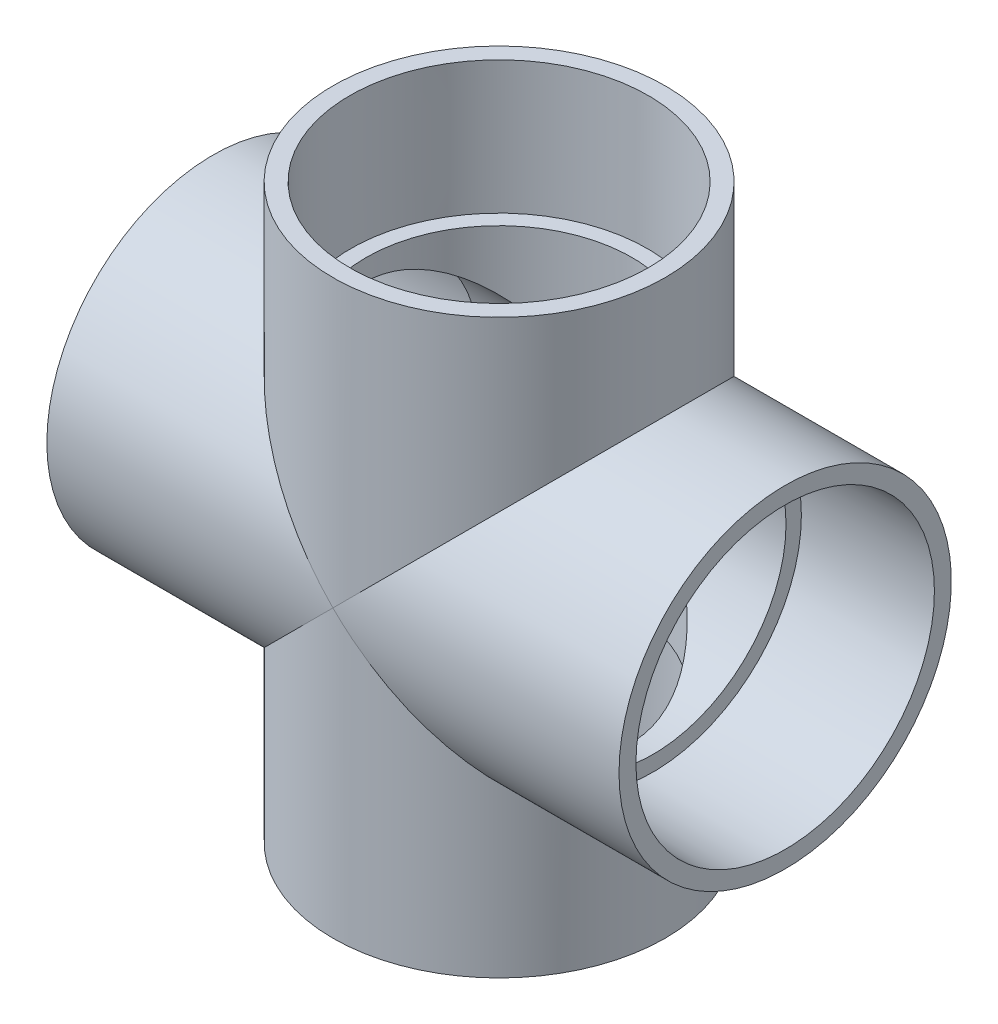
SolidWorks part; units mm, degrees
material "PVC Rigid"
ref_plane "Front Plane" through (0, 0, 0) normal (0, 0, 1) x (1, 0, 0)
ref_plane "Top Plane" through (0, 0, 0) normal (0, 1, 0) x (1, 0, 0)
ref_plane "Right Plane" through (0, 0, 0) normal (1, 0, 0) x (0, 0, -1)
sketch "Sketch0" plane through (0, 0, 0) normal (0, 0, 1) x (1, 0, 0)
  line L0 (-109.982, 0) -> (0, 0) construction
  line L1 (0, 0) -> (0, 109.982) construction
  line L2 (-59.182, 0) -> (0, 0) construction
  line L3 (0, 0) -> (0, 59.182) construction
  line L4 (-109.982, 63.881) -> (-109.982, -63.881) construction
  line L5 (-59.182, 57.0357) -> (-109.982, 57.3786) construction
  line L6 (-59.182, 57.0357) -> (-59.182, -57.0357) construction
  line L7 (-59.182, -57.0357) -> (-109.982, -57.3786) construction
  line L8 (-109.982, 57.3786) -> (-109.982, -57.3786) construction
  line L9 (-63.881, 109.982) -> (63.881, 109.982) construction
  line L10 (-57.3786, 109.982) -> (57.3786, 109.982) construction
  line L11 (57.3786, 109.982) -> (57.0357, 59.182) construction
  line L12 (57.0357, 59.182) -> (-57.0357, 59.182) construction
  line L13 (-57.0357, 59.182) -> (-57.3786, 109.982) construction
  line L14 (-59.182, 51.1302) -> (-59.182, -51.1302) construction
  line L15 (-109.982, 0) -> (-59.182, 0) construction
  line L16 (0, 109.982) -> (0, 59.182) construction
  line L17 (0, 0) -> (59.182, 0) construction
  line L18 (-51.1302, 59.182) -> (51.1302, 59.182) construction
  line L19 (59.182, 0) -> (109.982, 0) construction
  line L20 (0, 0) -> (0, -59.182) construction
  line L21 (0, -59.182) -> (0, -109.982) construction
  dimension "H" = 109.982
  dimension "G" = 59.182
  dimension "M" = 127.762
  dimension "OD A" = 114.7572
  dimension "OD B" = 114.0714
  dimension "ID" = 102.2604
sketch "Sketch1" plane through (0, 0, 0) normal (0, 0, 1) x (1, 0, 0)
  line L0 (-109.982, 0) -> (0, 0) construction
  line L1 (-109.982, 0) -> (0, 0) construction
  line L2 (0, 0) -> (0, -63.881) construction
  line L3 (-109.982, -63.881) -> (-59.182, -63.881)
  line L4 (-109.982, -63.881) -> (-109.982, -57.3786)
  line L5 (-109.982, -57.3786) -> (-59.182, -57.0357)
  line L6 (-59.182, -63.881) -> (-59.182, -57.0357)
  line L7 (-59.182, -63.881) -> (0, -63.881) construction
  line L8 (109.982, -57.3786) -> (59.182, -57.0357)
  line L9 (109.982, -63.881) -> (109.982, -57.3786)
  line L10 (59.182, -63.881) -> (59.182, -57.0357)
  line L11 (109.982, -63.881) -> (59.182, -63.881)
revolve "Revolve1" add sketch "Sketch1" angle 360 about L1
sketch "Sketch2" plane through (0, 0, 0) normal (0, 0, 1) x (1, 0, 0)
  line L0 (57.3786, 109.982) -> (57.0357, 59.182)
  line L1 (57.0357, 59.182) -> (63.881, 59.182)
  line L2 (63.881, 59.182) -> (63.881, 109.982)
  line L3 (63.881, 109.982) -> (57.3786, 109.982)
  line L4 (0, 0) -> (0, 109.982) construction
  line L5 (0, 0) -> (0, 109.982) construction
  line L6 (0, 0) -> (59.182, 0) construction
  line L7 (63.881, -109.982) -> (57.3786, -109.982)
  line L8 (63.881, -59.182) -> (63.881, -109.982)
  line L9 (57.0357, -59.182) -> (63.881, -59.182)
  line L10 (57.3786, -109.982) -> (57.0357, -59.182)
revolve "Revolve2" add sketch "Sketch2" angle 360 about L5
sketch "Sketch3" plane through (-59.182, 0, 0) normal (1, 0, 0) x (0, 0, -1)
  circle A0 centre (0, 0) radius 51.1302
  circle A1 centre (0, 0) radius 63.881
sketch "Sketch4" plane through (-59.182, 0, 0) normal (1, 0, 0) x (0, 0, -1)
  circle A0 centre (0, 0) radius 63.881 construction
  circle A1 centre (0, 0) radius 63.881
extrude "Boss-Extrude1" add sketch "Sketch4" along normal up to vertex
sketch "Sketch5" plane through (0, 59.182, 0) normal (0, -1, 0) x (1, 0, 0)
  circle A0 centre (0, 0) radius 63.881 construction
  circle A1 centre (0, 0) radius 63.881
extrude "Boss-Extrude2" add sketch "Sketch5" along normal up to vertex
sketch "Sketch6" plane through (0, 0, 0) normal (0, 0, 1) x (1, 0, 0)
  line L0 (-109.982, -57.3786) -> (-59.182, -57.0357)
  line L1 (-59.182, -57.0357) -> (-59.182, -51.1302)
  line L2 (-59.182, -51.1302) -> (59.182, -51.1302)
  line L3 (59.182, -51.7184) -> (59.182, 51.7184) construction
  line L4 (0, -51.1302) -> (0, 0) construction
  line L5 (59.182, -57.0357) -> (59.182, -51.1302)
  line L6 (109.982, -57.3786) -> (109.982, 57.3786) construction
  line L7 (109.982, -63.881) -> (109.982, 63.881) construction
  line L8 (109.982, -57.3786) -> (109.982, 0)
  line L9 (109.982, 0) -> (-109.982, 0)
  line L10 (-109.982, 0) -> (-109.982, -57.3786)
  line L11 (109.982, -57.3786) -> (59.182, -57.0357)
revolve "Cut-Revolve1" cut sketch "Sketch6" angle 360 about L9
sketch "Sketch7" plane through (0, 0, 0) normal (0, 0, 1) x (1, 0, 0)
  line L0 (57.3786, 109.982) -> (57.0357, 59.182)
  line L1 (57.0357, 59.182) -> (51.1302, 59.182)
  line L2 (51.1302, 59.182) -> (51.1302, -59.182)
  line L4 (51.1302, 0) -> (0, 0) construction
  line L5 (0, 109.982) -> (0, -109.982)
  line L6 (-63.881, 109.982) -> (63.881, 109.982) construction
  line L7 (0, 109.982) -> (57.3786, 109.982)
  line L8 (57.0357, -59.182) -> (51.1302, -59.182)
  line L9 (57.3786, -109.982) -> (57.0357, -59.182)
  line L10 (0, 0) -> (59.182, 0) construction
  line L11 (0, -109.982) -> (57.3786, -109.982)
revolve "Cut-Revolve2" cut sketch "Sketch7" angle 360 about L5
